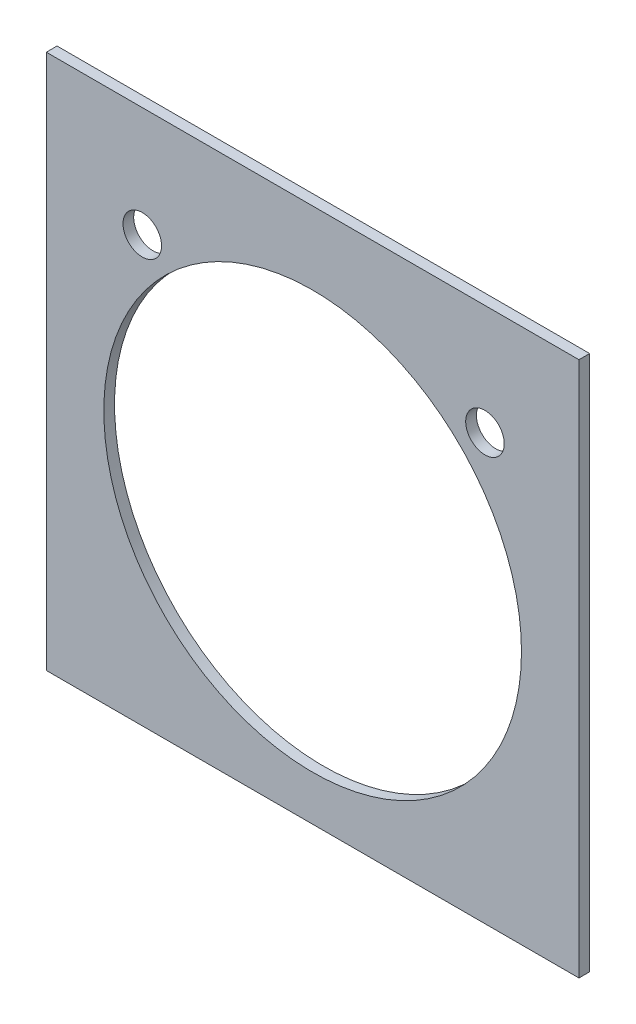
SolidWorks part; units mm, degrees
ref_plane "Front Plane" through (0, 0, 0) normal (0, 0, 1) x (1, 0, 0)
ref_plane "Top Plane" through (0, 0, 0) normal (0, 1, 0) x (1, 0, 0)
ref_plane "Right Plane" through (0, 0, 0) normal (1, 0, 0) x (0, 0, -1)
sketch "Sketch2" plane through (0, 0, 0) normal (0, 0, 1) x (1, 0, 0)
  line L1 (-24.8682, 25) -> (24.8682, 25)
  line L2 (-24.8682, 25) -> (-24.8682, -25)
  line L3 (-24.8682, -25) -> (24.8682, -25)
  line L4 (24.8682, 25) -> (24.8682, -25)
  line L5 (-24.8682, 25) -> (24.8682, -25) construction
  line L6 (-24.8682, -25) -> (24.8682, 25) construction
  point P0 (0, 0)
  dimension "D1" = 50
extrude "Boss-Extrude2" add sketch "Sketch2" along normal blind 1
sketch "Sketch3" plane through (0, 0, 1) normal (0, 0, 1) x (1, 0, 0)
  line L0 (-33.6615, 18.2) -> (33.6615, 18.2) construction
  line L3 (24.8682, 25) -> (-24.8682, 25) construction
  circle A0 centre (0, -1.3) radius 19.5
  point P6 (0, 18.2)
  dimension "D1" = 39
  dimension "D2" = 6.8
extrude "Cut-Extrude1" cut sketch "Sketch3" against normal blind 1
sketch "Sketch6" plane through (0, 0, 1) normal (0, 0, 1) x (1, 0, 0)
  line L0 (-29.6331, 14.7141) -> (33.2518, 14.7141) construction
  circle A0 centre (-15.909, 14.7141) radius 1.8
  circle A1 centre (16.091, 14.7141) radius 1.8
  dimension "D1" = 3.6
  dimension "D2" = 32
extrude "Cut-Extrude2" cut sketch "Sketch6" against normal through all
